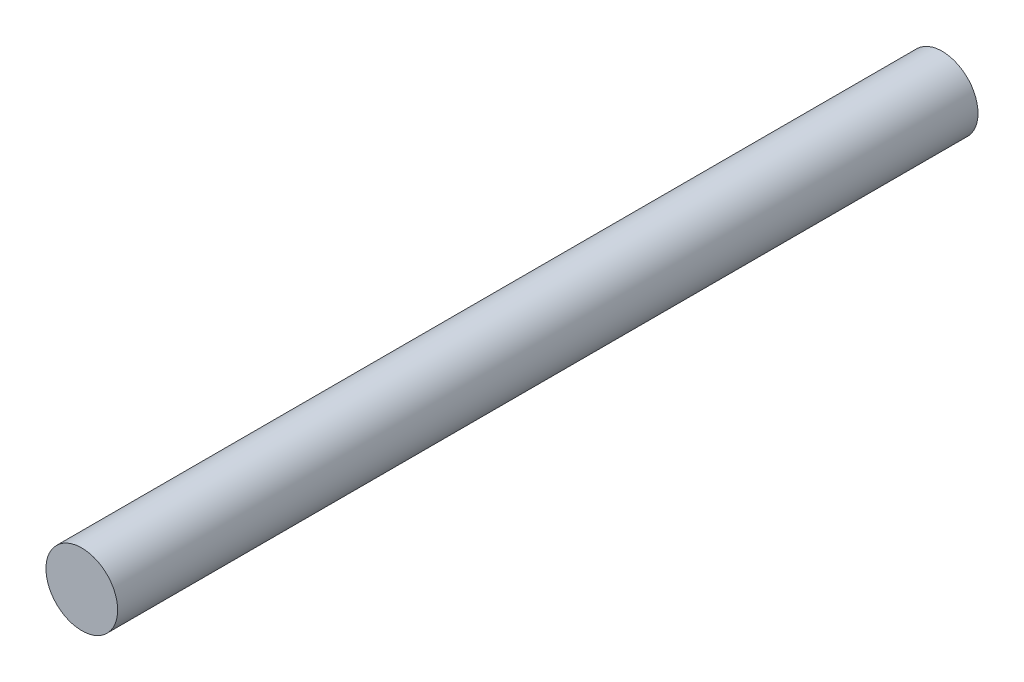
SolidWorks part; units mm, degrees
ref_plane "Front Plane" through (0, 0, 0) normal (0, 0, 1) x (1, 0, 0)
ref_plane "Top Plane" through (0, 0, 0) normal (0, 1, 0) x (1, 0, 0)
ref_plane "Right Plane" through (0, 0, 0) normal (1, 0, 0) x (0, 0, -1)
sketch "Sketch1" plane through (0, 0, 0) normal (0, 0, 1) x (1, 0, 0)
  circle A0 centre (0, 0) radius 12.5
  dimension "D1" = 25
extrude "Boss-Extrude1" add sketch "Sketch1" along normal blind 300
